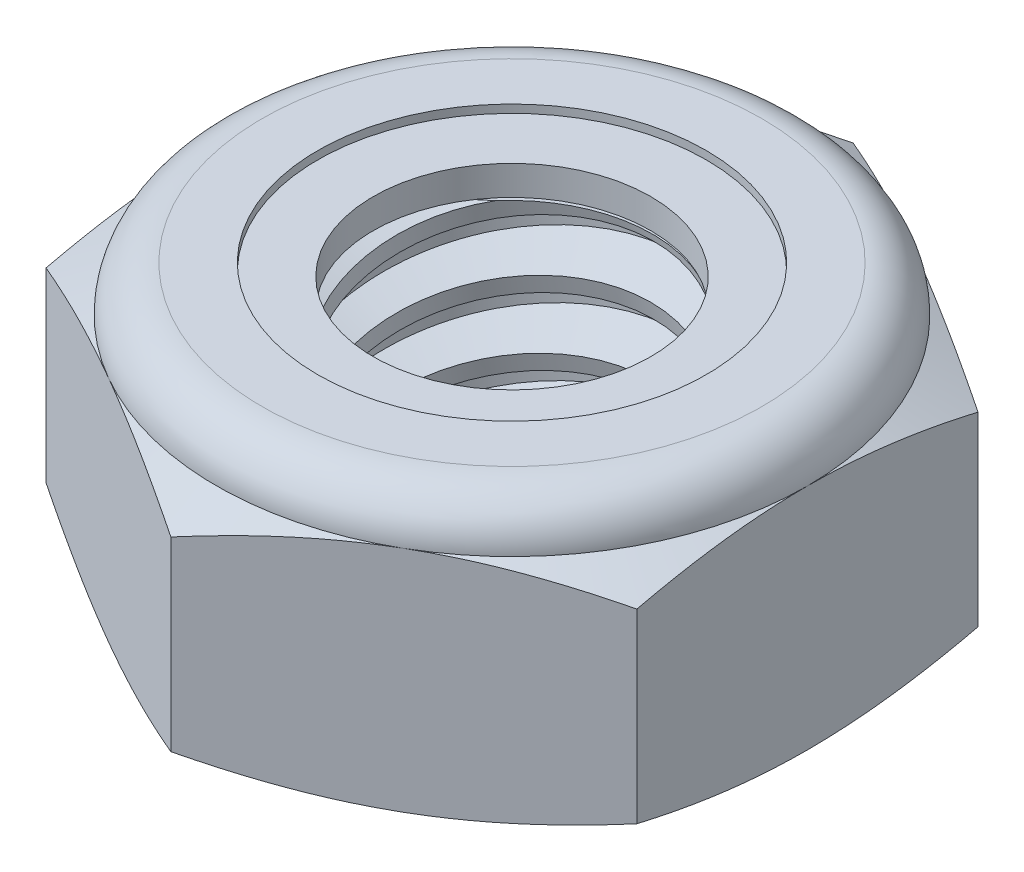
SolidWorks part; units mm, degrees
ref_plane "Front" through (0, 0, 0) normal (0, 0, 1) x (1, 0, 0)
ref_plane "Top" through (0, 0, 0) normal (0, 1, 0) x (1, 0, 0)
ref_plane "Right" through (0, 0, 0) normal (1, 0, 0) x (0, 0, -1)
sketch "Sketch1" plane through (0, 0, 0) normal (0, 1, 0) x (1, 0, 0)
  line L1 (0, 6.4158) -> (-5.5563, 3.2079)
  line L2 (-5.5563, 3.2079) -> (-5.5563, -3.2079)
  line L3 (-5.5563, -3.2079) -> (0, -6.4158)
  line L4 (0, -6.4158) -> (5.5562, -3.2079)
  line L5 (5.5562, -3.2079) -> (5.5562, 3.2079)
  line L6 (5.5562, 3.2079) -> (0, 6.4158)
  circle A0 centre (0, 0) radius 5.5563 construction
  dimension "Hex Flats" = 11.1125
extrude "Extrude1" add sketch "Sketch1" along normal blind 5.1594
sketch "Sketch2" plane through (0, 0, 0) normal (1, 0, 0) x (0, 0, -1)
  line L0 (-3.175, 0) -> (-3.175, 5.1594) construction
  line L1 (0, 0) -> (3.175, 0)
  line L2 (0, 0) -> (0, 5.1594)
  line L3 (0, 5.1594) -> (3.175, 5.1594)
  line L4 (3.175, 0) -> (3.175, 5.1594)
  line L5 (-3.2079, 5.1594) -> (3.2079, 5.1594) construction
  line L7 (0, -3.175) -> (0, 0) construction
  dimension "Thread Dia" = 6.35
revolve "Revolve1" add sketch "Sketch2" angle 360 about L7
sketch "Sketch3" plane through (0, 0, 0) normal (1, 0, 0) x (0, 0, -1)
  line L0 (3.175, 5.1594) -> (-3.175, 5.1594) construction
  line L1 (-3.175, 5.1594) -> (-3.175, 3.8894) construction
  line L2 (-3.175, 3.8894) -> (3.175, 5.1594) construction
  line L3 (3.175, 5.1594) -> (3.2061, 5.0037) construction
  line L4 (3.2061, 5.0037) -> (3.4241, 3.914)
  line L5 (3.4241, 3.914) -> (2.6722, 4.1684)
  line L6 (2.6722, 4.1684) -> (2.6099, 4.4797)
  line L7 (2.6099, 4.4797) -> (3.2061, 5.0037)
  line L8 (2.641, 4.3241) -> (3.3151, 4.4589) construction
  line L9 (3.175, 5.1594) -> (3.175, 4.4309) construction
  line L10 (3.175, 4.4309) -> (-3.175, 3.1609) construction
  line L11 (-3.175, 3.1609) -> (-3.175, 3.8894) construction
  line L12 (-0.2727, 5.1594) -> (0.2727, 2.4323) construction
  line L13 (-3.175, 0) -> (-3.175, 5.1594) construction
  line L14 (0, 5.1594) -> (3.175, 5.1594) construction
  line L15 (3.175, 0) -> (3.175, 5.1594) construction
  point P13 (0, 3.7959)
  dimension "D1" = 0.1588
  dimension "D2" = 0.3175
  dimension "Thread Pitch" = 1.27
  dimension "D4" = 60
  dimension "D5" = 1.27
revolve "Cut-Revolve1" cut sketch "Sketch3" angle 360 about L12
pattern_linear "LPattern1" count 4 spacing 1.27 along (0, -1, 0) count 2 spacing 1.27 along (0, 1, 0) of "Cut-Revolve1"
sketch "Sketch4" plane through (0, 0, 0) normal (1, 0, 0) x (0, 0, -1)
  line L0 (0, 5.1594) -> (3.175, 5.1594)
  line L1 (3.175, 5.1594) -> (2.6099, 4.8959)
  line L2 (2.6099, 4.8959) -> (2.6099, 0.2635)
  line L3 (2.6099, 0.2635) -> (3.175, 0)
  line L4 (3.175, 0) -> (0, 0)
  line L5 (0, 0) -> (0, 5.1594)
  line L6 (3.175, 0) -> (3.175, 5.1594) construction
  line L7 (0, 5.1594) -> (3.175, 5.1594) construction
  line L8 (0, 0) -> (3.175, 0) construction
  line L9 (0, 0) -> (0, 5.1594) construction
  line L10 (0, 5.1594) -> (0, 5.7829) construction
  dimension "D1" = 25
revolve "Cut-Revolve2" cut sketch "Sketch4" angle 360 about L10
combine bodies "Combine1" operation type subtract main body 112 bodies to subtract 111
sketch "Sketch5" plane through (0, 0, 0) normal (1, 0, 0) x (0, 0, -1)
  line L0 (0, 0) -> (5.5563, 0)
  line L1 (5.5563, 0) -> (6.4158, 0.4008)
  line L2 (6.4158, 0.4008) -> (6.4158, 3.8987)
  line L3 (6.4158, 3.8987) -> (5.5563, 4.2995)
  line L4 (4.6964, 5.1594) -> (4.6964, 6.4294)
  line L5 (4.6964, 6.4294) -> (7.6858, 6.4294)
  line L6 (7.6858, 6.4294) -> (7.6858, -1.27)
  line L7 (7.6858, -1.27) -> (0, -1.27)
  line L8 (0, -1.27) -> (0, 0)
  line L9 (5.5563, 4.2995) -> (5.5563, 0) construction
  line L10 (0, 0) -> (3.175, 0) construction
  line L13 (6.4158, 2.1497) -> (7.6858, 2.1497) construction
  line L14 (6.4158, 5.1594) -> (6.4158, 0) construction
  line L15 (0, 0) -> (0, 6.4294) construction
  line L20 (0, 6.4294) -> (4.6964, 6.4294) construction
  line L22 (0, 5.1594) -> (3.175, 5.1594) construction
  arc A0 (5.5563, 4.2995) -> (4.6964, 5.1594) centre (4.6964, 4.2995) ccw
  dimension "D1" = 25
  dimension "D2" = 1.27
  dimension "D3" = 5.1594
  dimension "D4" = 0.8599
revolve "Cut-Revolve3" cut sketch "Sketch5" angle 360 about L15
sketch "Sketch6" plane through (0, 0, 0) normal (1, 0, 0) x (0, 0, -1)
  line L0 (0, 4.2995) -> (5.4039, 4.2995)
  line L1 (4.6964, 5.007) -> (3.6531, 5.007)
  line L2 (0, 6.4294) -> (0, 4.2995)
  line L3 (3.6531, 6.4294) -> (0, 6.4294)
  line L4 (0, 6.4294) -> (4.6964, 6.4294) construction
  line L5 (0, 0) -> (0, 6.4294) construction
  line L6 (0, 6.4294) -> (0, 44.323) construction
  line L7 (3.6531, 5.007) -> (3.6531, 6.4294)
  line L8 (4.6964, 5.1594) -> (4.6964, 5.007) construction
  line L9 (3.6531, 5.007) -> (2.6099, 5.007) construction
  line L10 (2.6099, 5.007) -> (2.6099, 4.8959) construction
  arc A0 (5.4039, 4.2995) -> (4.6964, 5.007) centre (4.6964, 4.2995) ccw
  arc A1 (5.5563, 4.2995) -> (4.6964, 5.1594) centre (4.6964, 4.2995) ccw construction
  dimension "D1" = 0.1524
revolve "Cut-Revolve4" cut sketch "Sketch6" angle 360 about L6
sketch "Sketch7" plane through (0, 0, 0) normal (1, 0, 0) x (0, 0, -1)
  line L0 (2.6099, 4.3757) -> (5.323, 4.3757)
  line L1 (4.6964, 4.9308) -> (2.6099, 4.9308)
  line L2 (2.6099, 4.9308) -> (2.6099, 4.3757)
  line L3 (2.6099, 4.3757) -> (0, 4.3757) construction
  line L4 (0, 4.3757) -> (0, 4.9308) construction
  line L5 (0, 4.9308) -> (2.6099, 4.9308) construction
  line L6 (2.6099, 4.3757) -> (2.6099, 4.2995) construction
  line L7 (0, 4.2995) -> (5.4039, 4.2995) construction
  line L8 (4.6964, 4.9308) -> (4.6964, 5.007) construction
  arc A0 (5.323, 4.3757) -> (4.6964, 4.9308) centre (4.6964, 4.2995) ccw
  arc A2 (5.4039, 4.2995) -> (4.6964, 5.007) centre (4.6964, 4.2995) ccw construction
  dimension "D1" = 0.0762
revolve "Revolve2" add sketch "Sketch7" angle 360 about L4
equation "\"D1@Sketch3\"=\"Thread Pitch@Sketch3\"/8"
equation "\"D2@Sketch3\"=\"Thread Pitch@Sketch3\"/4"
equation "\"D5@Sketch3\"=\"Thread Pitch@Sketch3\""
equation "\"D4@LPattern1\"=\"Thread Pitch@Sketch3\""
equation "\"D3@LPattern1\"=\"Thread Pitch@Sketch3\""
equation "\"D1@LPattern1\"=\"Height@Extrude1\"/\"Thread Pitch@Sketch3\""
equation "\"D4@Sketch5\"=\"Height@Extrude1\"/6"
